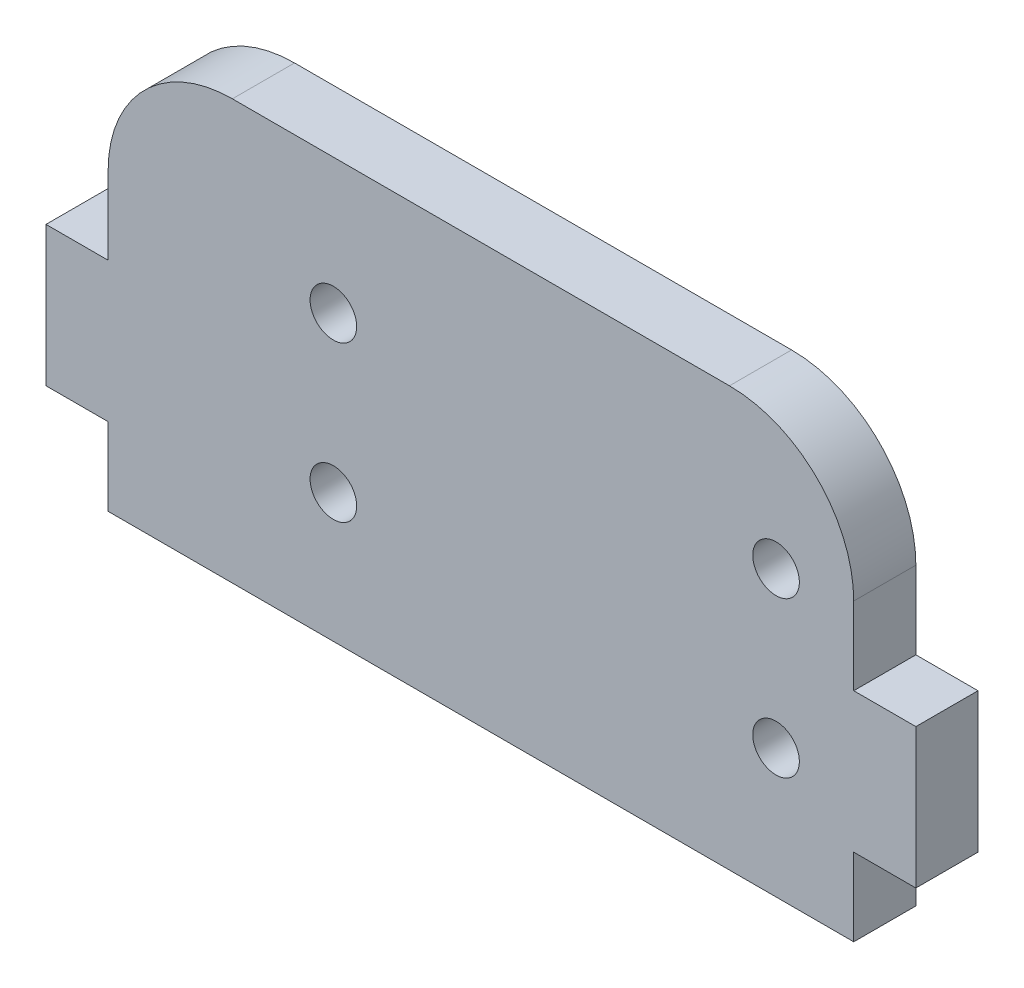
SolidWorks part; units mm, degrees
material "Beech"
ref_plane "Front Plane" through (0, 0, 0) normal (0, 0, 1) x (1, 0, 0)
ref_plane "Top Plane" through (0, 0, 0) normal (0, 1, 0) x (1, 0, 0)
ref_plane "Right Plane" through (0, 0, 0) normal (1, 0, 0) x (0, 0, -1)
sketch "Sketch1" plane through (0, 0, 0) normal (0, 0, 1) x (1, 0, 0)
  line L0 (4, 14) -> (0, 14)
  line L1 (0, 14) -> (0, 5)
  line L2 (0, 5) -> (4, 5)
  line L3 (4, 0) -> (4, 5)
  line L4 (4, 19) -> (4, 14)
  line L5 (52, 14) -> (56, 14)
  line L6 (56, 14) -> (56, 5)
  line L7 (56, 5) -> (52, 5)
  line L8 (52, 0) -> (52, 5)
  line L9 (52, 19) -> (52, 14)
  line L10 (44, 27) -> (12, 27)
  line L11 (4, 0) -> (52, 0)
  circle A0 centre (47, 18.3) radius 1.5
  circle A1 centre (47, 8.3) radius 1.5
  circle A2 centre (18.5, 18.3) radius 1.5
  circle A3 centre (18.5, 8.3) radius 1.5
  arc A4 (12, 27) -> (4, 19) centre (12, 19) ccw
  arc A5 (52, 19) -> (44, 27) centre (44, 19) ccw
extrude "Boss-Extrude1" add sketch "Sketch1" along normal blind 4
